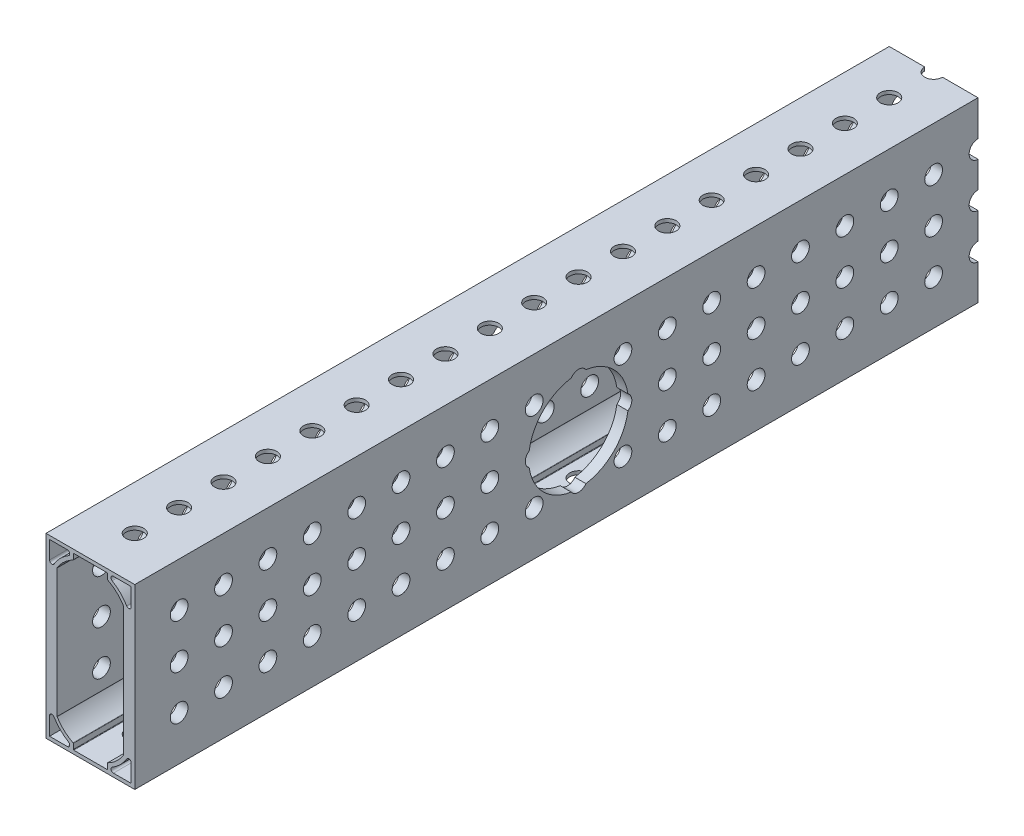
SolidWorks part; units mm, degrees
material "6061 Alloy"
ref_plane "Front Plane" through (0, 0, 0) normal (0, 0, 1) x (1, 0, 0)
ref_plane "Top Plane" through (0, 0, 0) normal (0, 1, 0) x (1, 0, 0)
ref_plane "Right Plane" through (0, 0, 0) normal (1, 0, 0) x (0, 0, -1)
other "Configuration Table"
ref_plane "Plane1" through (-12.7, 0, 0) normal (-1, 0, 0) x (0, -1, 0)
sketch "Sketch1" plane through (-12.7, 0, 0) normal (-1, 0, 0) x (0, -1, 0)
  line L0 (-25.4, -120.65) -> (25.4, -120.65)
  line L1 (25.4, -120.65) -> (25.4, 120.65)
  line L2 (25.4, 120.65) -> (-25.4, 120.65)
  line L3 (-25.4, 120.65) -> (-25.4, -120.65)
  line L4 (-25.4, -120.65) -> (25.4, 120.65) construction
  point P6 (0, 0)
  dimension "D1" = 50.8
  dimension "D2" = 241.3
extrude "Boss-Extrude1" add sketch "Sketch1" against normal blind 25.4
sketch "Sketch2" plane through (0, 0, -120.65) normal (0, 0, -1) x (-1, 0, 0)
  line L0 (-12.7, -12.573) -> (-12.7, -12.827)
  line L1 (-12.7, -12.827) -> (-12.573, -12.7)
  line L2 (-12.573, -12.7) -> (-12.7, -12.573)
  line L5 (-0.127, 0) -> (0.127, 0)
  line L6 (0.127, 0) -> (0, 0.127)
  line L7 (0, 0.127) -> (-0.127, 0)
  line L8 (-12.7, -25.4) -> (12.7, -25.4) construction
  line L9 (-12.7, 25.4) -> (-12.7, -25.4) construction
  line L10 (12.7, -12.827) -> (12.7, -12.573)
  line L11 (12.7, -12.573) -> (12.573, -12.7)
  line L12 (12.573, -12.7) -> (12.7, -12.827)
  line L13 (12.7, 25.4) -> (12.7, -25.4) construction
  line L17 (-12.7, 0.127) -> (-12.7, -0.127)
  line L18 (-12.7, -0.127) -> (-12.573, 0)
  line L19 (-12.573, 0) -> (-12.7, 0.127)
  line L20 (-12.7, 12.827) -> (-12.7, 12.573)
  line L21 (-12.7, 12.573) -> (-12.573, 12.7)
  line L22 (-12.573, 12.7) -> (-12.7, 12.827)
  line L23 (12.7, -0.127) -> (12.7, 0.127)
  line L24 (12.7, 0.127) -> (12.573, 0)
  line L25 (12.573, 0) -> (12.7, -0.127)
  line L26 (12.7, 12.573) -> (12.7, 12.827)
  line L27 (12.7, 12.827) -> (12.573, 12.7)
  line L28 (12.573, 12.7) -> (12.7, 12.573)
  line L29 (-0.127, 25.4) -> (0.127, 25.4)
  line L30 (0.127, 25.4) -> (0, 25.273)
  line L31 (0, 25.273) -> (-0.127, 25.4)
  line L32 (-12.7, 25.4) -> (12.7, 25.4) construction
  point P3 (-12.7, -12.7)
  point P10 (0, 0)
  point P31 (-12.7, 0)
  point P36 (-12.7, 12.7)
  dimension "D1" = 0.254
  dimension "D2" = 12.7
  dimension "D3" = 25.4
  dimension "D4" = 38.1
  dimension "D6" = 0.127
  dimension "D7" = 0.254
sketch "Sketch10" plane through (0, 0, 120.65) normal (0, 0, 1) x (1, 0, 0)
  line L0 (-11.684, 24.384) -> (-11.684, 19.2971)
  line L1 (-6.5971, 24.384) -> (-11.684, 24.384)
  line L2 (-12.7, -25.4) -> (-12.7, 25.4) construction
  line L18 (-12.7, -25.4) -> (-12.7, 25.4) construction
  line L19 (12.7, -25.4) -> (-12.7, -25.4) construction
  line L55 (0, 24.384) -> (-4.8895, 24.384)
  line L56 (-4.8895, 24.384) -> (-4.8895, 22.679)
  line L57 (-9.525, 18.4238) -> (-9.525, 0)
  line L70 (12.7, 25.4) -> (-12.7, 25.4) construction
  line L72 (12.7, 25.4) -> (-12.7, 25.4) construction
  line L73 (-9.525, 0) -> (0, 0)
  line L74 (0, 0) -> (0, 24.384)
  arc A0 (-11.684, 19.2971) -> (-10.3994, 18.9412) centre (-10.9924, 19.2971) ccw
  arc A1 (-10.3994, 18.9412) -> (-6.2412, 23.0994) centre (0, 12.7) cw
  arc A2 (-6.2412, 23.0994) -> (-6.5971, 24.384) centre (-6.5971, 23.6924) ccw
  arc A8 (-4.8895, 22.679) -> (-9.525, 18.4238) centre (0, 12.7) ccw
  dimension "D1" = 0.6916
  dimension "D2" = 12.1285
  dimension "D3" = 3.175
  dimension "D11" = 11.1125
  dimension "D12" = 1.016
  dimension "D4" = 1.016
  dimension "D5" = 2.3006
  dimension "D6" = 1.016
  dimension "D8" = 1.016
  dimension "D13" = 4.8895
extrude "Cut-Extrude9" cut sketch "Sketch10" against normal through all
mirror "Mirror1" about plane through (0, 0, 0) normal (0, 1, 0) of "Cut-Extrude9" second plane through (0, 0, 0) second plane normal (1, 0, 0)
sketch "Sketch17" plane through (12.7, 0, 0) normal (1, 0, 0) x (0, 0, -1)
  line L1 (-120.65, 25.4) -> (120.65, 25.4) construction
  line L2 (-120.65, -25.4) -> (-120.65, 25.4) construction
  circle A0 centre (-107.95, 12.7) radius 2.54
  dimension "D2" = 5.08
  dimension "D1" = 12.7
  dimension "D3" = 12.7
sketch "Sketch18" plane through (0, 25.4, 0) normal (0, 1, 0) x (1, 0, 0)
  line L1 (12.7, -120.65) -> (-12.7, -120.65) construction
  line L2 (12.7, -120.65) -> (12.7, 120.65) construction
  circle A0 centre (0, -107.95) radius 2.54
  dimension "D1" = 5.08
  dimension "D2" = 12.7
  dimension "D3" = 12.7
extrude "Cut-Extrude11" cut sketch "Sketch17" against normal through all and the other way through all
extrude "Cut-Extrude12" cut sketch "Sketch18" against normal through all
pattern_linear "LPattern1" count 19 spacing 12.7 along (0, 0, -1) of "Cut-Extrude12"
pattern_linear "LPattern2" count 20 spacing 12.7 along (0, 0, -1) count 3 spacing 12.7 along (0, -1, 0) of "Cut-Extrude11"
fillet "Fillet1" radius 0.127 12 edges at (-4.8895, -24.384, 0) (-4.8895, -22.679, 0) (-9.525, -18.4238, 0) (4.8895, -22.679, 0) (4.8895, -24.384, 0) (9.525, -18.4238, 0) (-4.8895, 22.679, 0) (-4.8895, 24.384, 0) (-9.525, 18.4238, 0) (4.8895, 24.384, 0) (4.8895, 22.679, 0) (9.525, 18.4238, 0)
sketch "Sketch19" plane through (-12.7, 0, 0) normal (-1, 0, 0) x (0, 0, 1)
  circle A0 centre (-6.35, 0) radius 14.2875
  dimension "D1" = 28.575
extrude "Cut-Extrude13" cut sketch "Sketch19" against normal through all
equation "\"Length\"= 9.5"
equation "\"D2@Sketch1\"=\"Length\""
